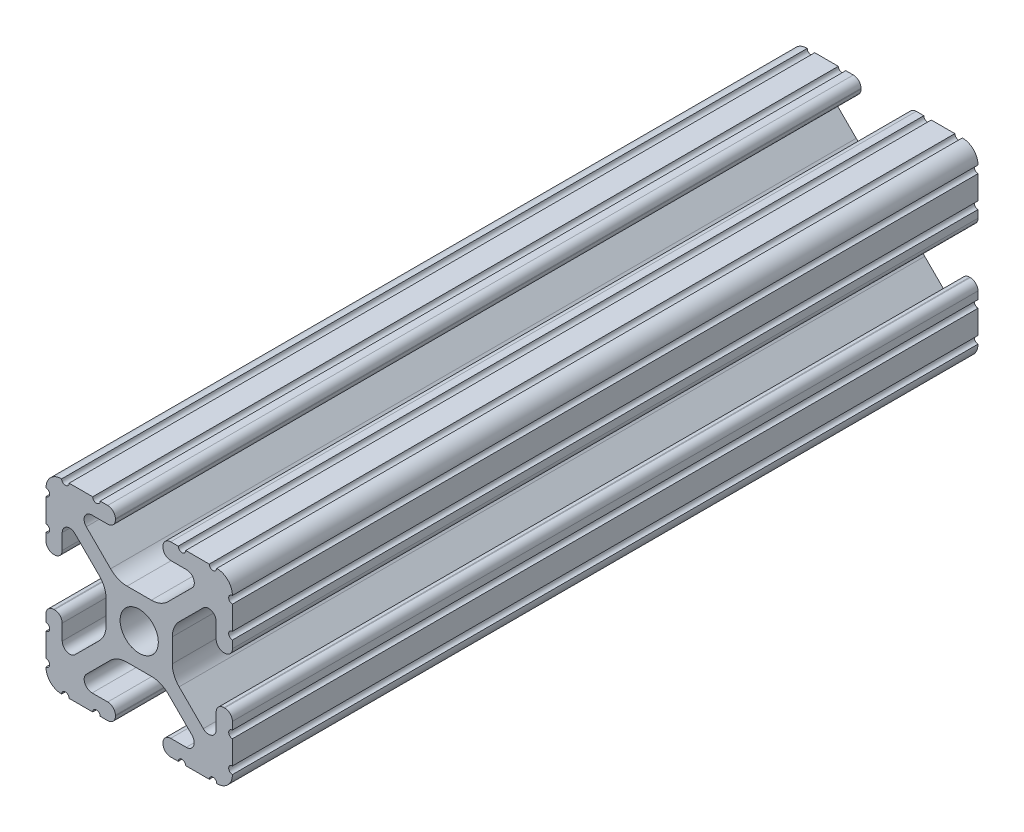
SolidWorks part; units mm, degrees
ref_plane "Front Plane" through (0, 0, 0) normal (0, 0, 1) x (1, 0, 0)
ref_plane "Top Plane" through (0, 0, 0) normal (0, 1, 0) x (1, 0, 0)
ref_plane "Right Plane" through (0, 0, 0) normal (1, 0, 0) x (0, 0, -1)
sketch "Sketch1" plane through (0, 0, 0) normal (0, 0, 1) x (1, 0, 0)
  line L88 (-7.1797, -8.6452) -> (-3.9523, -5.4237)
  line L89 (-1.7093, -4.4958) -> (1.7093, -4.4958)
  line L90 (3.9523, -5.4237) -> (7.1797, -8.6452)
  line L91 (6.4164, -10.4902) -> (4.2875, -10.4902)
  line L92 (3.2385, -11.5392) -> (3.2385, -11.651)
  line L93 (4.2875, -12.7) -> (5.3171, -12.7)
  line L94 (6.3331, -12.7) -> (9.5504, -12.7)
  line L95 (12.7, -9.5504) -> (12.7, -6.3331)
  line L96 (12.7, -5.3171) -> (12.7, -4.2875)
  line L97 (11.651, -3.2385) -> (11.5392, -3.2385)
  line L98 (10.4902, -4.2875) -> (10.4902, -6.4021)
  line L99 (8.7371, -7.1294) -> (5.441, -3.8408)
  line L100 (4.5085, -1.5932) -> (4.5085, 1.5932)
  line L101 (5.441, 3.8408) -> (8.7371, 7.1294)
  line L102 (10.4902, 6.4021) -> (10.4902, 4.2875)
  line L103 (11.5392, 3.2385) -> (11.651, 3.2385)
  line L104 (12.7, 4.2875) -> (12.7, 5.3171)
  line L105 (12.7, 6.3331) -> (12.7, 9.5504)
  line L106 (9.5504, 12.7) -> (6.3331, 12.7)
  line L107 (5.3171, 12.7) -> (4.2875, 12.7)
  line L108 (3.2385, 11.651) -> (3.2385, 11.5392)
  line L109 (4.2875, 10.4902) -> (6.4768, 10.4902)
  line L110 (7.207, 8.7244) -> (3.8983, 5.4232)
  line L111 (1.6558, 4.4958) -> (-1.6558, 4.4958)
  line L112 (-3.8983, 5.4232) -> (-7.207, 8.7244)
  line L113 (-6.4768, 10.4902) -> (-4.2875, 10.4902)
  line L114 (-3.2385, 11.5392) -> (-3.2385, 11.651)
  line L115 (-4.2875, 12.7) -> (-5.3171, 12.7)
  line L116 (-6.3331, 12.7) -> (-9.5504, 12.7)
  line L117 (-12.7, 9.5504) -> (-12.7, 6.3331)
  line L118 (-12.7, 5.3171) -> (-12.7, 4.2875)
  line L119 (-11.651, 3.2385) -> (-11.5392, 3.2385)
  line L120 (-10.4902, 4.2875) -> (-10.4902, 6.4021)
  line L121 (-8.7371, 7.1294) -> (-5.441, 3.8408)
  line L122 (-4.5085, 1.5932) -> (-4.5085, -1.5932)
  line L123 (-5.441, -3.8408) -> (-8.7371, -7.1294)
  line L124 (-10.4902, -6.4021) -> (-10.4902, -4.2875)
  line L125 (-11.5392, -3.2385) -> (-11.651, -3.2385)
  line L126 (-12.7, -4.2875) -> (-12.7, -5.3171)
  line L127 (-12.7, -6.3331) -> (-12.7, -9.5504)
  line L128 (-9.5504, -12.7) -> (-6.3331, -12.7)
  line L129 (-5.3171, -12.7) -> (-4.2875, -12.7)
  line L130 (-3.2385, -11.651) -> (-3.2385, -11.5392)
  line L131 (-4.2875, -10.4902) -> (-6.4164, -10.4902)
  circle A1 centre (0, 0) radius 2.6035
  arc A104 (-7.1797, -8.6452) -> (-6.4164, -10.4902) centre (-6.4164, -9.4098) ccw
  arc A105 (-1.7093, -4.4958) -> (-3.9523, -5.4237) centre (-1.7093, -7.6708) ccw
  arc A106 (3.9523, -5.4237) -> (1.7093, -4.4958) centre (1.7093, -7.6708) ccw
  arc A107 (6.4164, -10.4902) -> (7.1797, -8.6452) centre (6.4164, -9.4098) ccw
  arc A108 (4.2875, -10.4902) -> (3.2385, -11.5392) centre (4.2875, -11.5392) ccw
  arc A109 (3.2385, -11.651) -> (4.2875, -12.7) centre (4.2875, -11.651) ccw
  arc A110 (6.3331, -12.7) -> (5.3171, -12.7) centre (5.8251, -12.7) ccw
  arc A111 (10.5664, -12.6998) -> (9.5504, -12.7) centre (10.0584, -12.7) ccw
  arc A112 (10.5664, -12.6998) -> (12.6998, -10.5664) centre (10.5918, -10.5918) ccw
  arc A113 (12.7, -9.5504) -> (12.6998, -10.5664) centre (12.7, -10.0584) ccw
  arc A114 (12.7, -5.3171) -> (12.7, -6.3331) centre (12.7, -5.8251) ccw
  arc A115 (12.7, -4.2875) -> (11.651, -3.2385) centre (11.651, -4.2875) ccw
  arc A116 (11.5392, -3.2385) -> (10.4902, -4.2875) centre (11.5392, -4.2875) ccw
  arc A117 (8.7371, -7.1294) -> (10.4902, -6.4021) centre (9.4628, -6.4021) ccw
  arc A118 (4.5085, -1.5932) -> (5.441, -3.8408) centre (7.6835, -1.5932) ccw
  arc A119 (5.441, 3.8408) -> (4.5085, 1.5932) centre (7.6835, 1.5932) ccw
  arc A120 (10.4902, 6.4021) -> (8.7371, 7.1294) centre (9.4628, 6.4021) ccw
  arc A121 (10.4902, 4.2875) -> (11.5392, 3.2385) centre (11.5392, 4.2875) ccw
  arc A122 (11.651, 3.2385) -> (12.7, 4.2875) centre (11.651, 4.2875) ccw
  arc A123 (12.7, 6.3331) -> (12.7, 5.3171) centre (12.7, 5.8251) ccw
  arc A124 (12.6998, 10.5664) -> (12.7, 9.5504) centre (12.7, 10.0584) ccw
  arc A125 (12.6998, 10.5664) -> (10.5664, 12.6998) centre (10.5918, 10.5918) ccw
  arc A126 (9.5504, 12.7) -> (10.5664, 12.6998) centre (10.0584, 12.7) ccw
  arc A127 (5.3171, 12.7) -> (6.3331, 12.7) centre (5.8251, 12.7) ccw
  arc A128 (4.2875, 12.7) -> (3.2385, 11.651) centre (4.2875, 11.651) ccw
  arc A129 (3.2385, 11.5392) -> (4.2875, 10.4902) centre (4.2875, 11.5392) ccw
  arc A130 (7.207, 8.7244) -> (6.4768, 10.4902) centre (6.4768, 9.4563) ccw
  arc A131 (1.6558, 4.4958) -> (3.8983, 5.4232) centre (1.6558, 7.6708) ccw
  arc A132 (-3.8983, 5.4232) -> (-1.6558, 4.4958) centre (-1.6558, 7.6708) ccw
  arc A133 (-6.4768, 10.4902) -> (-7.207, 8.7244) centre (-6.4768, 9.4563) ccw
  arc A134 (-4.2875, 10.4902) -> (-3.2385, 11.5392) centre (-4.2875, 11.5392) ccw
  arc A135 (-3.2385, 11.651) -> (-4.2875, 12.7) centre (-4.2875, 11.651) ccw
  arc A136 (-6.3331, 12.7) -> (-5.3171, 12.7) centre (-5.8251, 12.7) ccw
  arc A137 (-10.5664, 12.6998) -> (-9.5504, 12.7) centre (-10.0584, 12.7) ccw
  arc A138 (-10.5664, 12.6998) -> (-12.6998, 10.5664) centre (-10.5918, 10.5918) ccw
  arc A139 (-12.7, 9.5504) -> (-12.6998, 10.5664) centre (-12.7, 10.0584) ccw
  arc A140 (-12.7, 5.3171) -> (-12.7, 6.3331) centre (-12.7, 5.8251) ccw
  arc A141 (-12.7, 4.2875) -> (-11.651, 3.2385) centre (-11.651, 4.2875) ccw
  arc A142 (-11.5392, 3.2385) -> (-10.4902, 4.2875) centre (-11.5392, 4.2875) ccw
  arc A143 (-8.7371, 7.1294) -> (-10.4902, 6.4021) centre (-9.4628, 6.4021) ccw
  arc A144 (-4.5085, 1.5932) -> (-5.441, 3.8408) centre (-7.6835, 1.5932) ccw
  arc A145 (-5.441, -3.8408) -> (-4.5085, -1.5932) centre (-7.6835, -1.5932) ccw
  arc A146 (-10.4902, -6.4021) -> (-8.7371, -7.1294) centre (-9.4628, -6.4021) ccw
  arc A147 (-10.4902, -4.2875) -> (-11.5392, -3.2385) centre (-11.5392, -4.2875) ccw
  arc A148 (-11.651, -3.2385) -> (-12.7, -4.2875) centre (-11.651, -4.2875) ccw
  arc A149 (-12.7, -6.3331) -> (-12.7, -5.3171) centre (-12.7, -5.8251) ccw
  arc A150 (-12.6998, -10.5664) -> (-12.7, -9.5504) centre (-12.7, -10.0584) ccw
  arc A151 (-12.6998, -10.5664) -> (-10.5664, -12.6998) centre (-10.5918, -10.5918) ccw
  arc A152 (-9.5504, -12.7) -> (-10.5664, -12.6998) centre (-10.0584, -12.7) ccw
  arc A153 (-5.3171, -12.7) -> (-6.3331, -12.7) centre (-5.8251, -12.7) ccw
  arc A154 (-4.2875, -12.7) -> (-3.2385, -11.651) centre (-4.2875, -11.651) ccw
  arc A155 (-3.2385, -11.5392) -> (-4.2875, -10.4902) centre (-4.2875, -11.5392) ccw
extrude "Boss-Extrude1" add sketch "Sketch1" along normal mid plane 101.6
